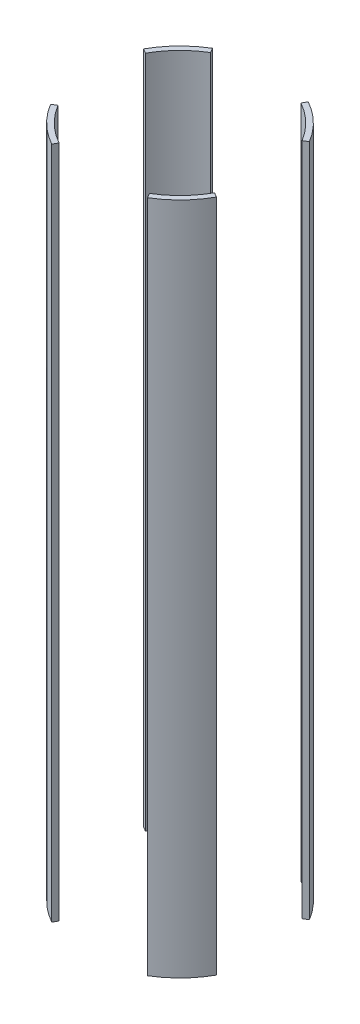
SolidWorks part; units mm, degrees
material "6061-T6 (SS)"
ref_plane "Front Plane" through (0, 0, 0) normal (0, 0, 1) x (1, 0, 0)
ref_plane "Top Plane" through (0, 0, 0) normal (0, 1, 0) x (1, 0, 0)
ref_plane "Right Plane" through (0, 0, 0) normal (1, 0, 0) x (0, 0, -1)
sketch "Sketch2" plane through (0, 0, 0) normal (0, 1, 0) x (1, 0, 0)
  circle A0 centre (0, 0) radius 88.9
  circle A1 centre (0, 0) radius 83.82
  dimension "D1" = 177.8
  dimension "D2" = 167.64
extrude "Boss-Extrude1" add sketch "Sketch2" along normal mid plane 635
sketch "Sketch3" plane through (0, 0, 0) normal (0, 1, 0) x (1, 0, 0)
  line L0 (0, 0) -> (169.6618, 101.6776)
  line L1 (-58.1167, 96.9749) -> (0, 0)
  line L2 (0, 0) -> (53.9, 96.9749)
  line L3 (53.9, 96.9749) -> (-58.1167, 96.9749)
  line L4 (0, 0) -> (70.9917, -118.4586)
  line L5 (70.9917, -118.4586) -> (-65.8409, -118.4586)
  line L6 (-65.8409, -118.4586) -> (0, 0)
  line L7 (169.6618, 101.6776) -> (169.6618, -94.3004)
  line L8 (169.6618, -94.3004) -> (0, 0)
  line L9 (0, 0) -> (-123.7413, 68.7771)
  line L10 (-123.7413, 68.7771) -> (-123.7413, -74.1577)
  line L11 (-123.7413, -74.1577) -> (0, 0)
  dimension "D1" = 60
  dimension "D2" = 60
  dimension "D3" = 60
  dimension "D4" = 60
  dimension "D5" = 30
  dimension "D6" = 30
extrude "Cut-Extrude1" cut sketch "Sketch3" against normal through all both and the other way through all contours L8 L7 L0 | L2 L3 L1 | L10 L11 L9 | L6 L5 L4
equation "\"D1@Boss-Extrude1\"=3*12"
